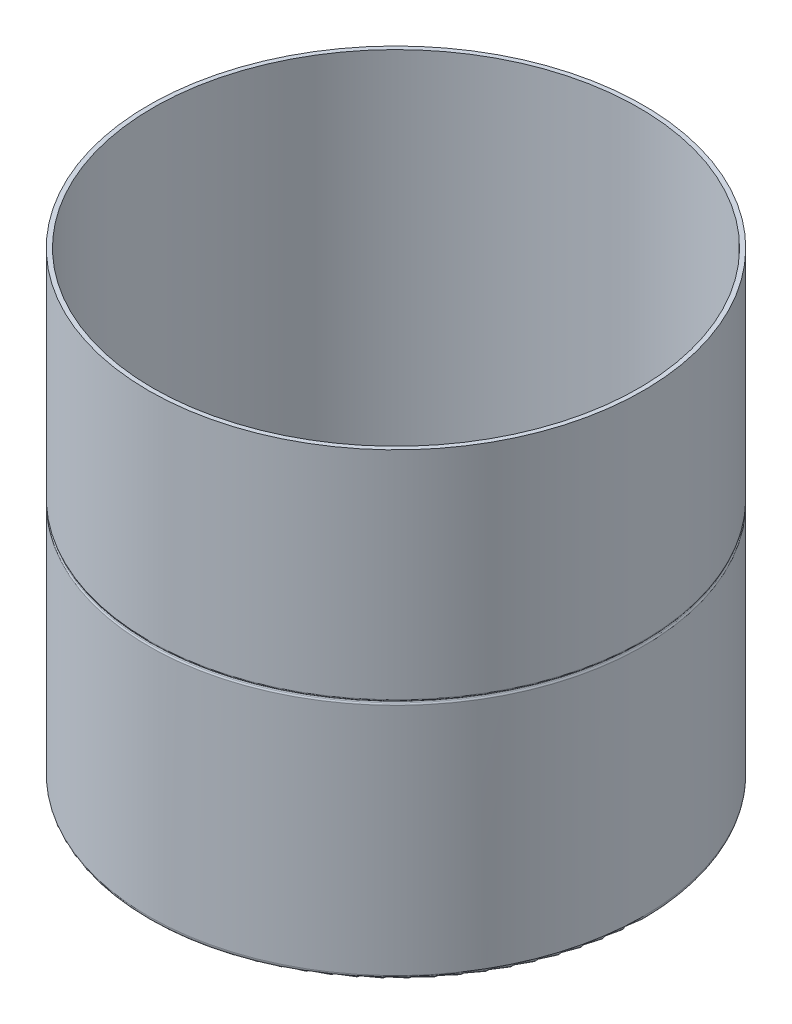
SolidWorks part; units mm, degrees
ref_plane "Front Plane" through (0, 0, 0) normal (0, 0, 1) x (1, 0, 0)
ref_plane "Top Plane" through (0, 0, 0) normal (0, 1, 0) x (1, 0, 0)
ref_plane "Right Plane" through (0, 0, 0) normal (1, 0, 0) x (0, 0, -1)
sketch "Sketch1" plane through (0, 0, 0) normal (0, 1, 0) x (1, 0, 0)
  circle A0 centre (0, 0) radius 56.5
extrude "Boss-Extrude1" add sketch "Sketch1" along normal blind 105 contours A0
sketch "Sketch2" plane through (0, 105, 0) normal (0, 1, 0) x (1, 0, 0)
  circle A0 centre (0, 0) radius 55.5
extrude "Cut-Extrude1" cut sketch "Sketch2" against normal blind 100
sketch "Sketch3" plane through (0, 0, 0) normal (0, -1, 0) x (1, 0, 0)
  circle A0 centre (0, 0) radius 25
extrude "Cut-Extrude2" cut sketch "Sketch3" against normal blind 5 contours A0
sketch "Sketch4" plane through (0, 0, 0) normal (0, -1, 0) x (1, 0, 0)
  circle A1 centre (44, 0) radius 2.5
  circle A2 centre (-44, 0) radius 2.5
extrude "Cut-Extrude3" cut sketch "Sketch4" against normal blind 5
ref_axis "Axis1" through (0, 105, 0) along (0, -1, 0)
sketch "Sketch6" plane through (0, 105, 0) normal (0, 1, 0) x (1, 0, 0)
  line L0 (0, 55.5) -> (0, 56.5)
  circle A0 centre (0, 0) radius 55.5 construction
  circle A1 centre (0, 0) radius 56.5 construction
ref_plane "Plane1" through (0, 0, 0) normal (1, 0, 0) x (0, 0, -1)
sketch "Sketch8" plane through (0, 0, 0) normal (1, 0, 0) x (0, 0, -1)
  line L1 (56.5, 0) -> (56.5, 105) construction
  circle A0 centre (56.5, 55) radius 0.25
revolve "Cut-Revolve2" cut sketch "Sketch8" angle 360 about axis through (0, 105, 0) along (0, -1, 0)
fillet "Fillet1" radius 2 1 edges at (0, 0, -25)
fillet "Fillet2" radius 1 1 edges at (0, 0, 56.5)
fillet "Fillet3" radius 0.5 1 edges at (0, 54.75, 56.5)
fillet "Fillet4" radius 0.5 1 edges at (0, 55.25, -56.5)
